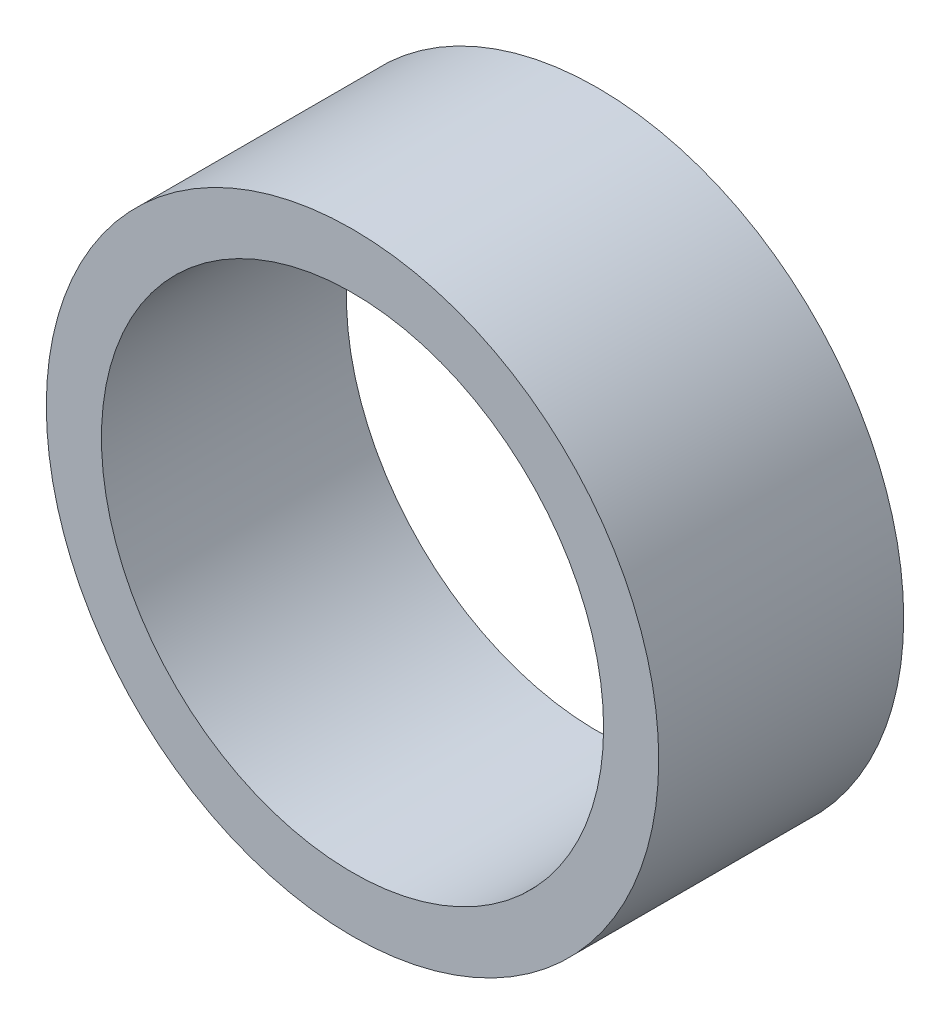
SolidWorks part; units mm, degrees
material "AISI 1045 钢，冷拔"
ref_plane "前视基准面" through (0, 0, 0) normal (0, 0, 1) x (1, 0, 0)
ref_plane "上视基准面" through (0, 0, 0) normal (0, 1, 0) x (1, 0, 0)
ref_plane "右视基准面" through (0, 0, 0) normal (1, 0, 0) x (0, 0, -1)
sketch "草图1" plane through (0, 0, 0) normal (0, 0, 1) x (1, 0, 0)
  circle A0 centre (-86.9476, 24.6003) radius 20.5
  circle A1 centre (-86.9476, 24.6003) radius 25
  dimension "D1" = 41
  dimension "D2" = 50
extrude "凸台-拉伸1" add sketch "草图1" along normal blind 20
